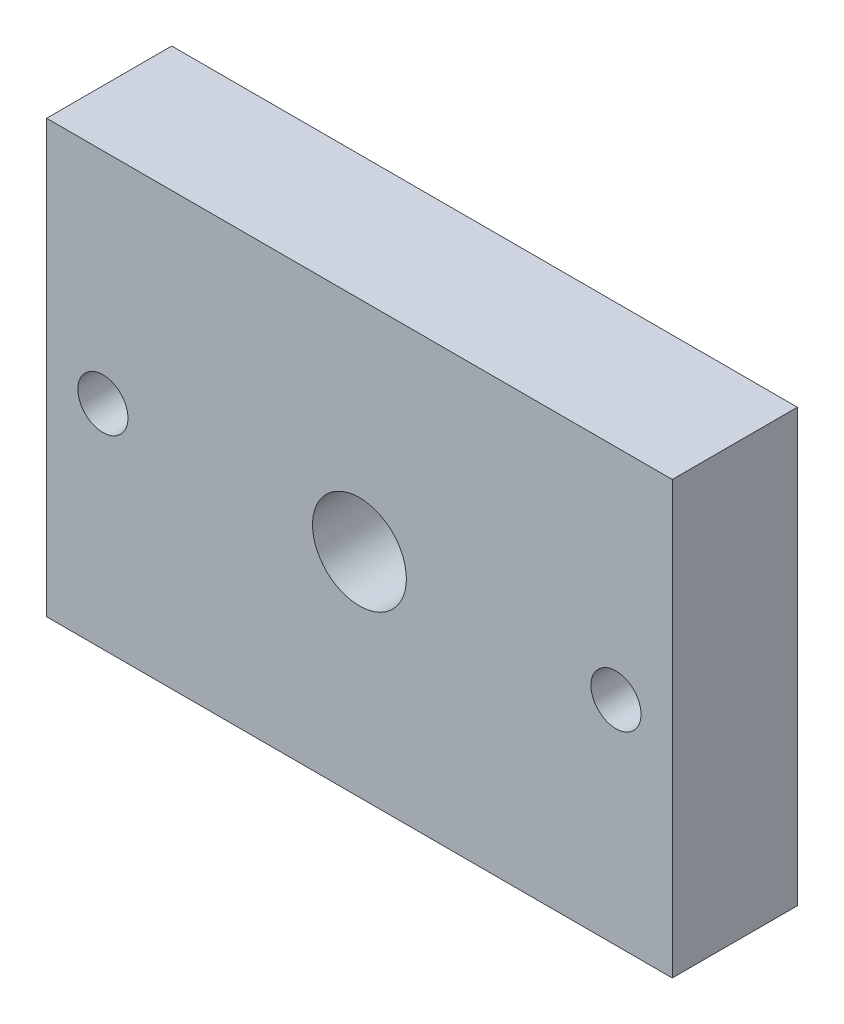
SolidWorks part; units mm, degrees
ref_plane "Płaszczyzna przednia" through (0, 0, 0) normal (0, 0, 1) x (1, 0, 0)
ref_plane "Płaszczyzna górna" through (0, 0, 0) normal (0, 1, 0) x (1, 0, 0)
ref_plane "Płaszczyzna prawa" through (0, 0, 0) normal (1, 0, 0) x (0, 0, -1)
sketch "Sketch1" plane through (0, 0, 0) normal (0, 0, 1) x (1, 0, 0)
  line L1 (-50, -35) -> (50, -35)
  line L2 (-50, -35) -> (-50, 35)
  line L3 (-50, 35) -> (50, 35)
  line L4 (50, -35) -> (50, 35)
  line L5 (-50, -35) -> (50, 35) construction
  line L6 (-50, 35) -> (50, -35) construction
  point P0 (0, 0)
  dimension "D1" = 100
  dimension "D2" = 70
extrude "Boss-Extrude1" add sketch "Sketch1" along normal blind 20
sketch "Sketch2" plane through (0, 0, 0) normal (0, 0, 1) x (1, 0, 0)
  line L0 (-50, 0) -> (50, 0) construction
  line L1 (-50, 35) -> (-50, -35) construction
  line L2 (50, -35) -> (50, 35) construction
  circle A0 centre (-41, 0) radius 4
  circle A1 centre (41, 0) radius 4
  dimension "D3" = 8
  dimension "D4" = 8
  dimension "D1" = 9
  dimension "D2" = 9
extrude "Cut-Extrude1" cut sketch "Sketch2" along normal through all both and the other way through all
sketch "Sketch3" plane through (0, 0, 20) normal (0, 0, 1) x (1, 0, 0)
  circle A0 centre (0, 0) radius 7.5
  dimension "D1" = 15
extrude "Cut-Extrude2" cut sketch "Sketch3" against normal blind 15
sketch "Sketch4" plane through (0, 0, 0) normal (0, 0, 1) x (1, 0, 0)
  line L0 (50, -35) -> (50, 35) construction
  line L1 (-50, -35) -> (50, -35)
  line L2 (-50, -35) -> (-50, -34)
  line L3 (-50, -34) -> (50, -34)
  line L4 (50, -35) -> (50, -34)
  dimension "D1" = 1
extrude "Cut-Extrude3" cut sketch "Sketch4" along normal through all both and the other way through all
